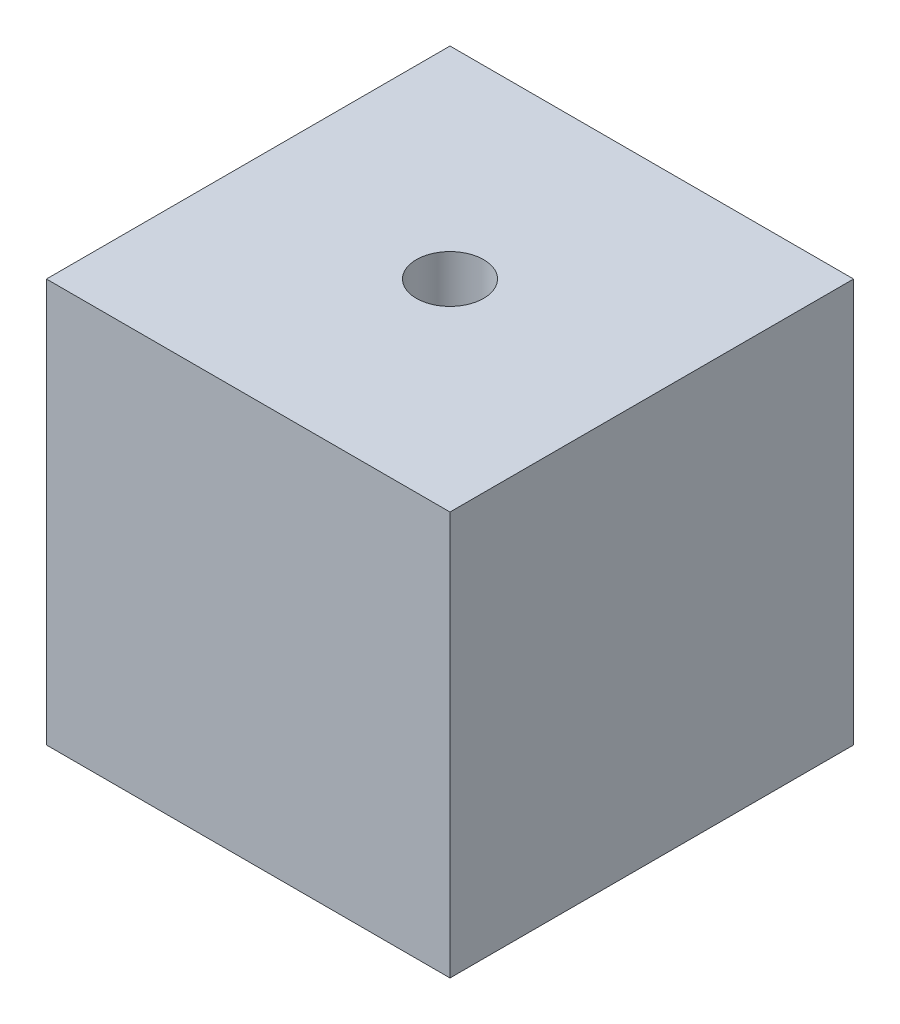
SolidWorks part; units mm, degrees
ref_plane "Front Plane" through (0, 0, 0) normal (0, 0, 1) x (1, 0, 0)
ref_plane "Top Plane" through (0, 0, 0) normal (0, 1, 0) x (1, 0, 0)
ref_plane "Right Plane" through (0, 0, 0) normal (1, 0, 0) x (0, 0, -1)
sketch "Sketch1" plane through (0, 0, 0) normal (0, 0, 1) x (1, 0, 0)
  line L1 (0, 0) -> (38.1, 0)
  line L2 (0, 0) -> (0, 38.1)
  line L3 (0, 38.1) -> (38.1, 38.1)
  line L4 (38.1, 0) -> (38.1, 38.1)
  dimension "D1" = 38.1
  dimension "D2" = 38.1
extrude "Boss-Extrude1" add sketch "Sketch1" along normal blind 38.1
sketch "Sketch2" plane through (0, 38.1, 0) normal (0, 1, 0) x (1, 0, 0)
  line L0 (0, 0) -> (38.1, -38.1) construction
  line L1 (38.1, 0) -> (0, -38.1) construction
  circle A0 centre (19.05, -19.05) radius 3.175
  dimension "D1" = 6.35
extrude "Cut-Extrude1" cut sketch "Sketch2" against normal through all
